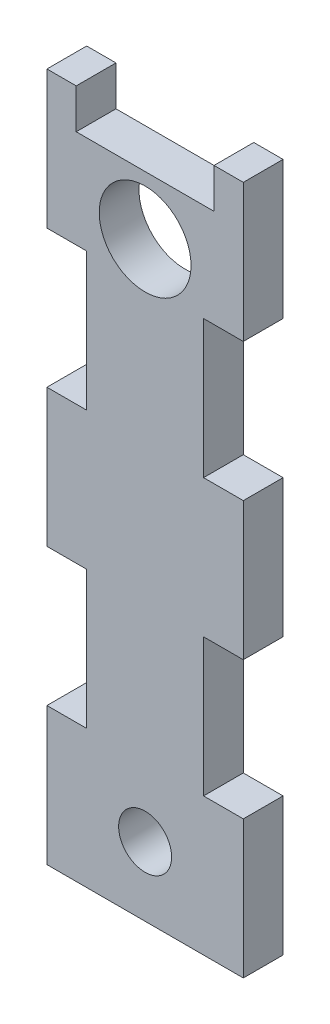
SolidWorks part; units mm, degrees
ref_plane "Front Plane" through (0, 0, 0) normal (0, 0, 1) x (1, 0, 0)
ref_plane "Top Plane" through (0, 0, 0) normal (0, 1, 0) x (1, 0, 0)
ref_plane "Right Plane" through (0, 0, 0) normal (1, 0, 0) x (0, 0, -1)
sketch "Sketch1" plane through (0, 0, 0) normal (0, 0, 1) x (1, 0, 0)
  line L0 (0, -33.02) -> (9.525, -33.02)
  line L1 (0, 0) -> (47.05, 0)
  line L2 (0, 0) -> (0, -165.1)
  line L3 (0, -165.1) -> (47.05, -165.1)
  line L4 (47.05, 0) -> (47.05, -165.1)
  line L5 (9.525, -9.525) -> (37.525, -9.525)
  line L6 (9.525, -9.525) -> (9.525, -37.525)
  line L7 (9.525, -37.525) -> (37.525, -37.525)
  line L8 (37.525, -9.525) -> (37.525, -37.525)
  line L9 (9.525, -33.02) -> (9.525, -66.04)
  line L10 (9.525, -66.04) -> (0, -66.04)
  line L11 (0, -132.08) -> (9.525, -132.08)
  line L12 (9.525, -132.08) -> (9.525, -99.06)
  line L13 (9.525, -99.06) -> (0, -99.06)
  line L14 (23.525, 0) -> (23.525, -165.1) construction
  line L15 (47.05, -132.08) -> (37.525, -132.08)
  line L16 (37.525, -132.08) -> (37.525, -99.06)
  line L17 (37.525, -99.06) -> (47.05, -99.06)
  line L18 (37.525, -66.04) -> (47.05, -66.04)
  line L19 (37.525, -33.02) -> (37.525, -66.04)
  line L20 (47.05, -33.02) -> (37.525, -33.02)
  line L21 (7.015, 0) -> (7.015, -9.525)
  line L22 (40.035, 0) -> (40.035, -9.525)
  line L23 (7.015, -9.525) -> (40.035, -9.525)
  circle A0 centre (23.525, -23.525) radius 11
  point P12 (23.525, -9.525)
  point P13 (9.525, -23.525)
  dimension "D7" = 22
  dimension "D1" = 165.1
  dimension "D2" = 47.05
  dimension "D3" = 9.525
  dimension "D4" = 9.525
  dimension "D5" = 9.525
  dimension "D6" = 28
  dimension "D8" = 33.02
  dimension "D9" = 33.02
  dimension "D10" = 33.02
  dimension "D11" = 9.525
  dimension "D12" = 33.02
  dimension "D13" = 33.02
  dimension "D14" = 7.015
extrude "Boss-Extrude1" add sketch "Sketch1" along normal blind 9.525 contours L7 L14 L3 L4 L15 L16 L17 L18 L19 | L14 L7 L9 L10 L2 L13 L12 L11 L3 | L23 L8 L20 L4 L1 L22 | L23 L21 L1 L2 L0 L6 | L14 L5 L6 L7 A0 | L23 L14 A0 L7 L8
sketch "Sketch2" plane through (0, 0, 0) normal (0, 0, -1) x (-1, 0, 0)
  line L48 (-7.015, -9.525) -> (-40.035, -9.525)
  line L49 (-40.035, -9.525) -> (-40.035, 0)
  line L50 (-40.035, 0) -> (-47.05, 0)
  line L51 (-47.05, 0) -> (-47.05, -33.02)
  line L52 (-47.05, -33.02) -> (-37.525, -33.02)
  line L53 (-37.525, -33.02) -> (-37.525, -66.04)
  line L54 (-37.525, -66.04) -> (-47.05, -66.04)
  line L55 (-47.05, -66.04) -> (-47.05, -99.06)
  line L56 (-47.05, -99.06) -> (-37.525, -99.06)
  line L57 (-37.525, -99.06) -> (-37.525, -132.08)
  line L58 (-37.525, -132.08) -> (-47.05, -132.08)
  line L59 (-47.05, -132.08) -> (-47.05, -165.1)
  line L60 (-47.05, -165.1) -> (0, -165.1)
  line L61 (0, -165.1) -> (0, -132.08)
  line L62 (0, -132.08) -> (-9.525, -132.08)
  line L63 (-9.525, -132.08) -> (-9.525, -99.06)
  line L64 (-9.525, -99.06) -> (0, -99.06)
  line L65 (0, -99.06) -> (0, -66.04)
  line L66 (0, -66.04) -> (-9.525, -66.04)
  line L67 (-9.525, -66.04) -> (-9.525, -33.02)
  line L68 (-9.525, -33.02) -> (0, -33.02)
  line L69 (0, -33.02) -> (0, 0)
  line L70 (0, 0) -> (-7.015, 0)
  line L71 (-7.015, 0) -> (-7.015, -9.525)
  line L72 (-7.015, -9.525) -> (-40.035, -9.525)
  line L73 (-40.035, -9.525) -> (-40.035, 0)
  line L74 (-40.035, 0) -> (-47.05, 0)
  line L75 (-47.05, 0) -> (-47.05, -33.02)
  line L76 (-47.05, -33.02) -> (-37.525, -33.02)
  line L77 (-37.525, -33.02) -> (-37.525, -66.04)
  line L78 (-37.525, -66.04) -> (-47.05, -66.04)
  line L79 (-47.05, -66.04) -> (-47.05, -99.06)
  line L80 (-47.05, -99.06) -> (-37.525, -99.06)
  line L81 (-37.525, -99.06) -> (-37.525, -132.08)
  line L82 (-37.525, -132.08) -> (-47.05, -132.08)
  line L83 (-47.05, -132.08) -> (-47.05, -165.1)
  line L84 (-47.05, -165.1) -> (0, -165.1)
  line L85 (0, -165.1) -> (0, -132.08)
  line L86 (0, -132.08) -> (-9.525, -132.08)
  line L87 (-9.525, -132.08) -> (-9.525, -99.06)
  line L88 (-9.525, -99.06) -> (0, -99.06)
  line L89 (0, -99.06) -> (0, -66.04)
  line L90 (0, -66.04) -> (-9.525, -66.04)
  line L91 (-9.525, -66.04) -> (-9.525, -33.02)
  line L92 (-9.525, -33.02) -> (0, -33.02)
  line L93 (0, -33.02) -> (0, 0)
  line L94 (0, 0) -> (-7.015, 0)
  line L95 (-7.015, 0) -> (-7.015, -9.525)
  dimension "D1" = 0
sketch "Sketch3" plane through (0, 0, 0) normal (0, 0, -1) x (-1, 0, 0)
  line L0 (0, -165.1) -> (-47.05, -165.1) construction
  line L1 (-47.05, -132.08) -> (-47.05, -165.1) construction
  circle A0 centre (-23.525, -148.59) radius 6.35
  point P2 (0, 0)
  point P3 (-23.525, -165.1)
  point P4 (-47.05, -148.59)
  dimension "D1" = 12.7
extrude "Cut-Extrude1" cut sketch "Sketch3" against normal through all both and the other way through all
